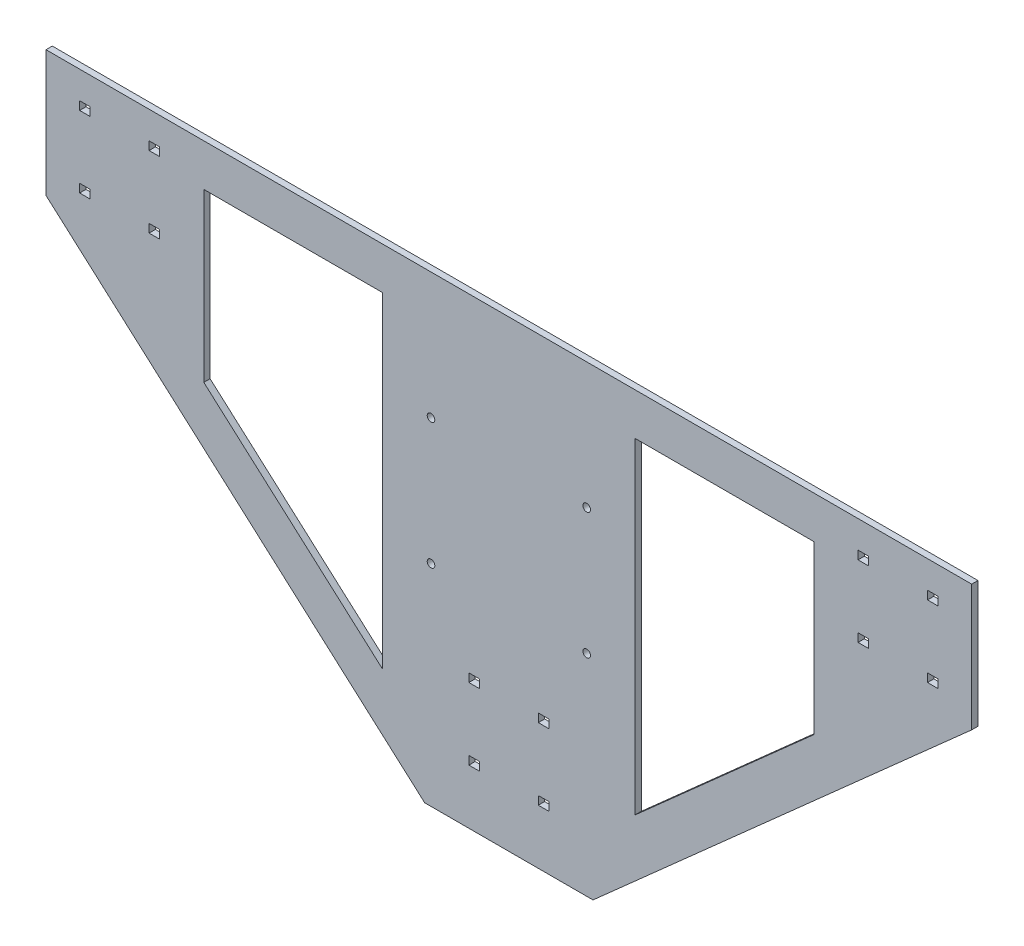
SolidWorks part; units mm, degrees
ref_plane "Plan de face" through (0, 0, 0) normal (0, 0, 1) x (1, 0, 0)
ref_plane "Plan de dessus" through (0, 0, 0) normal (0, 1, 0) x (1, 0, 0)
ref_plane "Plan de droite" through (0, 0, 0) normal (1, 0, 0) x (0, 0, -1)
sketch "Esquisse1" plane through (0, 0, 0) normal (0, 0, 1) x (1, 0, 0)
  line L0 (-220, 50) -> (-40, -110)
  line L1 (-220, 110) -> (220, 110)
  line L2 (-220, 110) -> (-220, -110) construction
  line L3 (-220, -110) -> (220, -110) construction
  line L4 (220, 110) -> (220, -110) construction
  line L5 (-220, 110) -> (220, -110) construction
  line L6 (-220, -110) -> (220, 110) construction
  line L7 (40, -110) -> (220, 50)
  line L8 (-220, 110) -> (-220, 50)
  line L9 (220, 110) -> (220, 50)
  line L10 (-40, -110) -> (40, -110)
  point P0 (0, 0)
  dimension "D1" = 440
  dimension "D2" = 220
  dimension "D3" = 180
  dimension "D4" = 60
  dimension "D5" = 60
  dimension "D6" = 180
extrude "Boss.-Extru.1" add sketch "Esquisse1" along normal blind 3 contours L3 L7 L4 L1 L2 L0
sketch "Esquisse2" plane through (0, 0, 0) normal (0, 0, -1) x (-1, 0, 0)
  line L0 (0, 110) -> (0, -110) construction
  line L3 (-220, 0) -> (220, 0) construction
  line L6 (-199, 95) -> (-171, 95) construction
  line L7 (-204, 97) -> (-199, 97)
  line L8 (-204, 97) -> (-204, 93)
  line L9 (-204, 93) -> (-199, 93)
  line L10 (-199, 97) -> (-199, 93)
  line L11 (-204, 97) -> (-199, 93) construction
  line L12 (-204, 93) -> (-199, 97) construction
  line L13 (-171, 97) -> (-166, 97)
  line L14 (-171, 97) -> (-171, 93)
  line L15 (-171, 93) -> (-166, 93)
  line L16 (-166, 97) -> (-166, 93)
  line L17 (-171, 97) -> (-166, 93) construction
  line L18 (-171, 93) -> (-166, 97) construction
  line L19 (-185, 94) -> (-185, 62) construction
  line L20 (-201, 78) -> (-169, 78) construction
  line L21 (-171, 63) -> (-166, 63)
  line L22 (-166, 59) -> (-166, 63)
  line L23 (-171, 59) -> (-166, 59)
  line L24 (-171, 59) -> (-171, 63)
  line L25 (-204, 59) -> (-199, 59)
  line L26 (-204, 59) -> (-204, 63)
  line L27 (-204, 63) -> (-199, 63)
  line L28 (-199, 59) -> (-199, 63)
  line L29 (171, 59) -> (171, 63)
  line L30 (171, 59) -> (166, 59)
  line L31 (166, 59) -> (166, 63)
  line L32 (171, 63) -> (166, 63)
  line L33 (199, 59) -> (199, 63)
  line L34 (204, 63) -> (199, 63)
  line L35 (204, 59) -> (204, 63)
  line L36 (204, 59) -> (199, 59)
  line L37 (166, 97) -> (166, 93)
  line L38 (171, 93) -> (166, 93)
  line L39 (171, 97) -> (166, 97)
  line L40 (171, 97) -> (171, 93)
  line L41 (204, 93) -> (199, 93)
  line L42 (199, 97) -> (199, 93)
  line L43 (204, 97) -> (199, 97)
  line L44 (204, 97) -> (204, 93)
  line L77 (-14, -50) -> (-14, -46)
  line L78 (-14, -50) -> (-19, -50)
  line L79 (-19, -50) -> (-19, -46)
  line L80 (-14, -46) -> (-19, -46)
  line L81 (14, -50) -> (19, -50)
  line L82 (19, -50) -> (19, -46)
  line L83 (14, -46) -> (19, -46)
  line L84 (14, -50) -> (14, -46)
  line L85 (-33.4039, -65) -> (42.5507, -65) construction
  line L86 (14, -80) -> (14, -84)
  line L87 (14, -84) -> (19, -84)
  line L88 (19, -80) -> (19, -84)
  line L89 (14, -80) -> (19, -80)
  line L90 (-14, -80) -> (-19, -80)
  line L91 (-19, -80) -> (-19, -84)
  line L92 (-14, -84) -> (-19, -84)
  line L93 (-14, -80) -> (-14, -84)
  line L95 (220, 110) -> (-220, 110) construction
  line L97 (-220, 110) -> (-220, 50) construction
  line L98 (40, -110) -> (-40, -110) construction
  line L99 (220, 110) -> (-220, 110) construction
  line L100 (220, 110) -> (220, -120.5017) construction
  circle A0 centre (-185, 78) radius 16 construction
  point P4 (0, 0)
  point P5 (0, 0)
  point P6 (0, 0)
  point P7 (32.5754, -65)
  point P10 (42.5507, -65)
  point P20 (-201.5, 95)
  point P25 (-168.5, 95)
  dimension "D1" = 32
  dimension "D2" = 32
  dimension "D3" = 35
  dimension "D4" = 28
  dimension "D5" = 5
  dimension "D6" = 4
  dimension "D7" = 5
  dimension "D8" = 4
  dimension "D9" = 15
  dimension "D10" = 14
  dimension "D11" = 4
  dimension "D12" = 5
  dimension "D13" = 60
  dimension "D14" = 14
  dimension "D15" = 15
  dimension "D16" = 220
  dimension "D17" = 110
extrude "Enlèv. mat.-Extru.1" cut sketch "Esquisse2" against normal blind 3
sketch "Esquisse4" plane through (0, 0, 3) normal (0, 0, 1) x (1, 0, 0)
  line L0 (0, 132.0704) -> (0, -144.2831) construction
  line L1 (-37, 50) -> (37, 50) construction
  line L2 (-37, -10) -> (37, -10) construction
  line L3 (-220, 110) -> (220, 110) construction
  line L4 (-37, 50) -> (-37, -10) construction
  circle A0 centre (-37, 50) radius 1.8
  circle A1 centre (37, 50) radius 1.8
  circle A2 centre (-37, -10) radius 1.8
  circle A3 centre (37, -10) radius 1.8
  dimension "D1" = 3.6
  dimension "D4" = 3.6
  dimension "D7" = 3.6
  dimension "D8" = 3.6
  dimension "D2" = 37
  dimension "D3" = 74
  dimension "D5" = 74
  dimension "D6" = 60
  dimension "D9" = 60
extrude "Enlèv. mat.-Extru.2" cut sketch "Esquisse4" against normal blind 3
sketch "Esquisse5" plane through (0, 0, 3) normal (0, 0, 1) x (1, 0, 0)
  line L1 (-145, 90) -> (-60, 90)
  line L2 (-145, 90) -> (-145, -65) construction
  line L3 (-145, -65) -> (-60, -65) construction
  line L4 (-60, 90) -> (-60, -65)
  line L5 (-220, 110) -> (-220, 50) construction
  line L6 (-220, 110) -> (220, 110) construction
  line L7 (-60, -65) -> (-145, 10.5556)
  line L8 (-145, 90) -> (-145, 10.5556)
  line L9 (0, 129.7689) -> (0, -126.0369) construction
  line L10 (145, 90) -> (60, 90)
  line L11 (60, 90) -> (60, -65)
  line L12 (60, -65) -> (145, 10.5556)
  line L13 (145, 90) -> (145, 10.5556)
  dimension "D1" = 75
  dimension "D2" = 20
  dimension "D3" = 85
  dimension "D4" = 155
  dimension "D5" = 113.7262
extrude "Enlèv. mat.-Extru.3" cut sketch "Esquisse5" against normal blind 3
